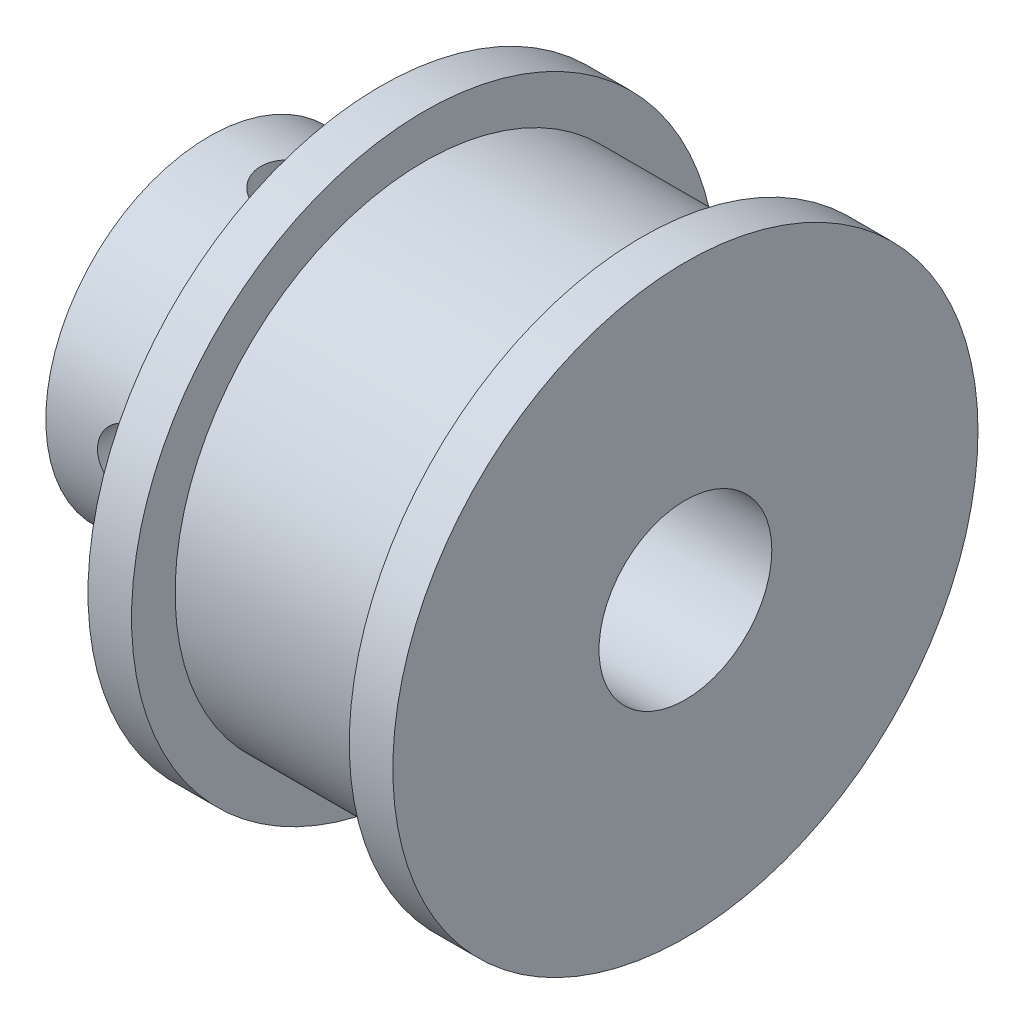
SolidWorks part; units mm, degrees
material "6061-T6 (SS)"
ref_plane "Front Plane" through (0, 0, 0) normal (0, 0, 1) x (1, 0, 0)
ref_plane "Top Plane" through (0, 0, 0) normal (0, 1, 0) x (1, 0, 0)
ref_plane "Right Plane" through (0, 0, 0) normal (1, 0, 0) x (0, 0, -1)
sketch "Sketch1" plane through (0, 0, 0) normal (0, 0, 1) x (1, 0, 0)
  line L0 (0, 3.175) -> (0, 6)
  line L1 (6.3, 10.75) -> (7.9, 10.75)
  line L2 (7.9, 10.75) -> (7.9, 9.15)
  line L3 (7.9, 9.15) -> (15.9, 9.15)
  line L4 (15.9, 9.15) -> (15.9, 10.75)
  line L5 (15.9, 10.75) -> (17.5, 10.75)
  line L6 (17.5, 10.75) -> (17.5, 3.175)
  line L7 (17.5, 3.175) -> (0, 3.175)
  line L8 (0, 0) -> (-7.6744, 0) construction
  line L9 (6.3, 10.75) -> (6.3, 6)
  line L10 (6.3, 6) -> (0, 6)
  dimension "D1" = 6.35
  dimension "D2" = 21.5
  dimension "D3" = 18.3
  dimension "D4" = 11.2
  dimension "D5" = 17.5
  dimension "D6" = 1.6
  dimension "D7" = 12
revolve "Revolve1" add sketch "Sketch1" angle 360 about L8
hole_wizard "M3x0.5 Tapped Hole1" positions "Sketch3" profile "Sketch2" tap size "M3x0.5" standard "ANSI Metric"
sketch "Sketch3" plane through (0, 0, 0) normal (0, 1, 0) x (1, 0, 0)
  line L0 (0, 0) -> (6.3, 0) construction
  line L2 (6.3, 6) -> (6.3, -6) construction
  point P8 (3.15, 0)
sketch "Sketch2" plane through (3.15, 0, 0) normal (1, 0, 0) x (0, 0, -1)
  line L0 (0, 0) -> (0, 10.75)
  line L1 (0, 10.75) -> (1.25, 10.75)
  line L2 (1.25, 10.75) -> (1.25, 0)
  line L5 (1.25, 0) -> (0, 0)
  line L11 (0, -6.35) -> (0, 107.95) construction
  dimension "Thread Major Dia." = 2.5
  dimension "Thru Tap Drill Depth" = 10.75
hole_wizard "M3x0.5 Tapped Hole2" positions "Sketch5" profile "Sketch4" tap size "M3x0.5" standard "ANSI Metric"
sketch "Sketch5" plane through (0, 0, 0) normal (0, 0, 1) x (1, 0, 0)
  line L0 (0, 0) -> (6.3, 0) construction
  line L2 (6.3, 10.75) -> (6.3, -10.75) construction
  point P7 (3.15, 0)
sketch "Sketch4" plane through (3.15, 0, 0) normal (1, 0, 0) x (0, 1, 0)
  line L0 (0, 0) -> (0, 10.75)
  line L1 (0, 10.75) -> (1.25, 10.75)
  line L2 (1.25, 10.75) -> (1.25, 0)
  line L5 (1.25, 0) -> (0, 0)
  line L11 (0, -6.35) -> (0, 107.95) construction
  dimension "Thread Major Dia." = 2.5
  dimension "Thru Tap Drill Depth" = 10.75
